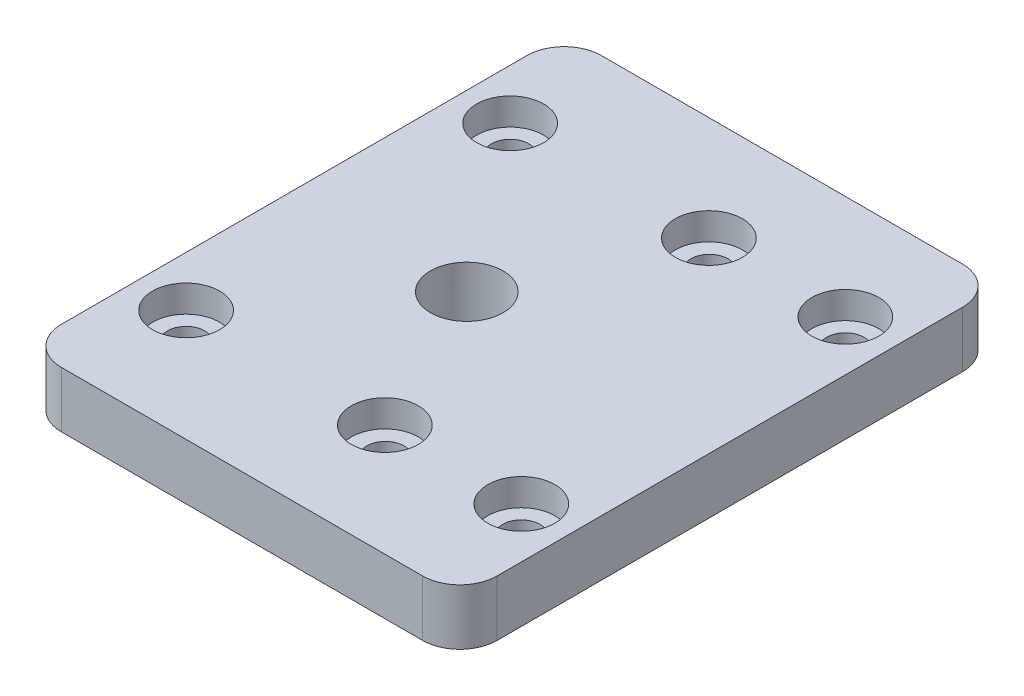
SolidWorks part; units mm, degrees
material "Custom Plastic"
ref_plane "Front Plane" through (0, 0, 0) normal (0, 0, 1) x (1, 0, 0)
ref_plane "Top Plane" through (0, 0, 0) normal (0, 1, 0) x (1, 0, 0)
ref_plane "Right Plane" through (0, 0, 0) normal (1, 0, 0) x (0, 0, -1)
sketch "Sketch1" plane through (0, 0, 0) normal (0, 1, 0) x (1, 0, 0)
  line L0 (-30.4611, 0) -> (33.997, 0) construction
  line L1 (-11.7, -14.5) -> (11.7, -14.5)
  line L2 (-11.7, -14.5) -> (-11.7, 14.5)
  line L3 (-11.7, 14.5) -> (11.7, 14.5)
  line L4 (11.7, -14.5) -> (11.7, 14.5)
  line L5 (-11.7, -14.5) -> (11.7, 14.5) construction
  line L6 (-11.7, 14.5) -> (11.7, -14.5) construction
  circle A0 centre (9, 8.9) radius 1
  circle A2 centre (9, -8.5) radius 1
  circle A3 centre (-9, -8.5) radius 1
  circle A5 centre (1.7, -8.5) radius 1
  spline S1 degree 3 poles (19.181, -14.2425) (19.8008, -12.3411) (17.8993, -11.7212) (17.2795, -13.6227) (16.6596, -15.5241) (18.5612, -16.144) (19.181, -14.2425) (19.8008, -12.3411) (17.8993, -11.7212) knots -0.5 0 0 0 0.5 0.5 0.5 1 1 1 1.5 1.5 1.5 weights 1 0.333333 0.333333 1 0.333333 0.333333 1 0.333333 0.333333 only from (19.181, -14.2425) to (19.181, -14.2425) construction
  spline S2 degree 3 poles (22.4885, -4.0962) (23.1083, -2.1947) (21.2068, -1.5749) (20.587, -3.4763) (19.9671, -5.3778) (21.8687, -5.9977) (22.4885, -4.0962) (23.1083, -2.1947) (21.2068, -1.5749) knots -0.5 0 0 0 0.5 0.5 0.5 1 1 1 1.5 1.5 1.5 weights 1 0.333333 0.333333 1 0.333333 0.333333 1 0.333333 0.333333 only from (22.4885, -4.0962) to (22.4885, -4.0962) construction
  spline S3 degree 3 poles (19.181, -14.2425) (19.8008, -12.3411) (17.8993, -11.7212) (17.2795, -13.6227) (16.6596, -15.5241) (18.5612, -16.144) (19.181, -14.2425) (19.8008, -12.3411) (17.8993, -11.7212) knots -0.5 0 0 0 0.5 0.5 0.5 1 1 1 1.5 1.5 1.5 weights 1 0.333333 0.333333 1 0.333333 0.333333 1 0.333333 0.333333 only from (19.181, -14.2425) to (19.181, -14.2425)
  spline S4 degree 3 poles (22.4885, -4.0962) (23.1083, -2.1947) (21.2068, -1.5749) (20.587, -3.4763) (19.9671, -5.3778) (21.8687, -5.9977) (22.4885, -4.0962) (23.1083, -2.1947) (21.2068, -1.5749) knots -0.5 0 0 0 0.5 0.5 0.5 1 1 1 1.5 1.5 1.5 weights 1 0.333333 0.333333 1 0.333333 0.333333 1 0.333333 0.333333 only from (22.4885, -4.0962) to (22.4885, -4.0962)
  point P0 (0, 0)
  point P6 (-9, 8.5)
  point P7 (9, 8.5)
  point P8 (9, 8.9)
  point P18 (1.7, 8.5)
  dimension "D7" = 17.4
  dimension "D8" = 18
  dimension "D10" = 2
  dimension "D1" = 29
  dimension "D2" = 23.4
  dimension "D3" = 6
  dimension "D4" = 6
  dimension "D5" = 18
  dimension "D6" = 2.7
  dimension "D9" = 10.7
extrude "Boss-Extrude1" add sketch "Sketch1" along normal blind 3
fillet "Fillet1" radius 2 4 edges at (11.7, 1.5, -14.5) (11.7, 1.5, 14.5) (-11.7, 1.5, 14.5) (-11.7, 1.5, -14.5)
sketch "Sketch5" plane through (0, 0, 0) normal (0, -1, 0) x (1, 0, 0)
  circle A0 centre (-2.1456, 3.6104) radius 2.5 construction
  circle A1 centre (-2.1456, 3.6104) radius 2.5 construction
  circle A2 centre (-2.1456, 3.6104) radius 1.44
  dimension "D1" = 2.88
extrude "Cut-Extrude3" cut sketch "Sketch5" against normal blind 10
sketch "Sketch7" plane through (0, 3, 0) normal (0, 1, 0) x (1, 0, 0)
  spline S0 degree 3 poles (19.181, -14.2425) (19.8008, -12.3411) (17.8993, -11.7212) (17.2795, -13.6227) (16.6596, -15.5241) (18.5612, -16.144) (19.181, -14.2425) (19.8008, -12.3411) (17.8993, -11.7212) knots -0.5 0 0 0 0.5 0.5 0.5 1 1 1 1.5 1.5 1.5 weights 1 0.333333 0.333333 1 0.333333 0.333333 1 0.333333 0.333333 only from (19.181, -14.2425) to (19.181, -14.2425) construction
  spline S1 degree 3 poles (22.4885, -4.0962) (23.1083, -2.1947) (21.2068, -1.5749) (20.587, -3.4763) (19.9671, -5.3778) (21.8687, -5.9977) (22.4885, -4.0962) (23.1083, -2.1947) (21.2068, -1.5749) knots -0.5 0 0 0 0.5 0.5 0.5 1 1 1 1.5 1.5 1.5 weights 1 0.333333 0.333333 1 0.333333 0.333333 1 0.333333 0.333333 only from (22.4885, -4.0962) to (22.4885, -4.0962) construction
  spline S2 degree 3 poles (19.181, -14.2425) (19.8008, -12.3411) (17.8993, -11.7212) (17.2795, -13.6227) (16.6596, -15.5241) (18.5612, -16.144) (19.181, -14.2425) (19.8008, -12.3411) (17.8993, -11.7212) knots -0.5 0 0 0 0.5 0.5 0.5 1 1 1 1.5 1.5 1.5 weights 1 0.333333 0.333333 1 0.333333 0.333333 1 0.333333 0.333333 only from (19.181, -14.2425) to (19.181, -14.2425)
  spline S3 degree 3 poles (22.4885, -4.0962) (23.1083, -2.1947) (21.2068, -1.5749) (20.587, -3.4763) (19.9671, -5.3778) (21.8687, -5.9977) (22.4885, -4.0962) (23.1083, -2.1947) (21.2068, -1.5749) knots -0.5 0 0 0 0.5 0.5 0.5 1 1 1 1.5 1.5 1.5 weights 1 0.333333 0.333333 1 0.333333 0.333333 1 0.333333 0.333333 only from (22.4885, -4.0962) to (22.4885, -4.0962)
extrude "Cut-Extrude4" cut sketch "Sketch7" against normal blind 10
sketch "Sketch8" plane through (0, 3, 0) normal (0, 1, 0) x (1, 0, 0)
  line L0 (24.633, 0) -> (-21.7502, 0) construction
  line L1 (1.7, -8.5) -> (1.7, 20.7764) construction
  line L2 (-9, -8.5) -> (-9, 21.3011) construction
  line L3 (9, -8.5) -> (9, 8.9) construction
  line L4 (14.3582, 8.9) -> (-23.7207, 8.9) construction
  circle A0 centre (1.7, 8.9) radius 1
  circle A1 centre (-9, 8.9) radius 1
  point P15 (1.7, 8.9)
  point P16 (-9, 8.9)
  dimension "D1" = 2
  dimension "D2" = 2
extrude "Cut-Extrude5" cut sketch "Sketch8" against normal blind 10
sketch "Sketch9" plane through (0, 3, 0) normal (0, 1, 0) x (1, 0, 0)
  circle A0 centre (-2.1456, -3.6104) radius 3.027
extrude "Boss-Extrude3" add sketch "Sketch9" against normal up to surface (3 mm away) up to face at (-9, 0, -9.9)
sketch "Sketch10" plane through (0, 3, 0) normal (0, 1, 0) x (1, 0, 0)
  circle A1 centre (-2.3282, -0.1) radius 1.5 construction
  circle A2 centre (-2.3282, -0.1) radius 1.95
  circle A3 centre (-2.3282, -0.1) radius 4 construction
  dimension "D1" = 3.9
extrude "Cut-Extrude6" cut sketch "Sketch10" against normal blind 10
sketch "Sketch11" plane through (0, 3, 0) normal (0, 1, 0) x (1, 0, 0)
  circle A0 centre (-9, -8.5) radius 1.8
  circle A1 centre (1.6718, -8.5) radius 1.8
  circle A2 centre (9, -8.5) radius 1.8
  circle A3 centre (9, 8.9) radius 1.8
  circle A4 centre (1.6718, 8.9) radius 1.8
  circle A5 centre (-9, 8.9) radius 1.8
  dimension "D1" = 3.6
  dimension "D2" = 3.6
  dimension "D3" = 3.6
  dimension "D4" = 3.6
  dimension "D5" = 3.6
  dimension "D6" = 3.6
extrude "Cut-Extrude7" cut sketch "Sketch11" against normal blind 1.45
